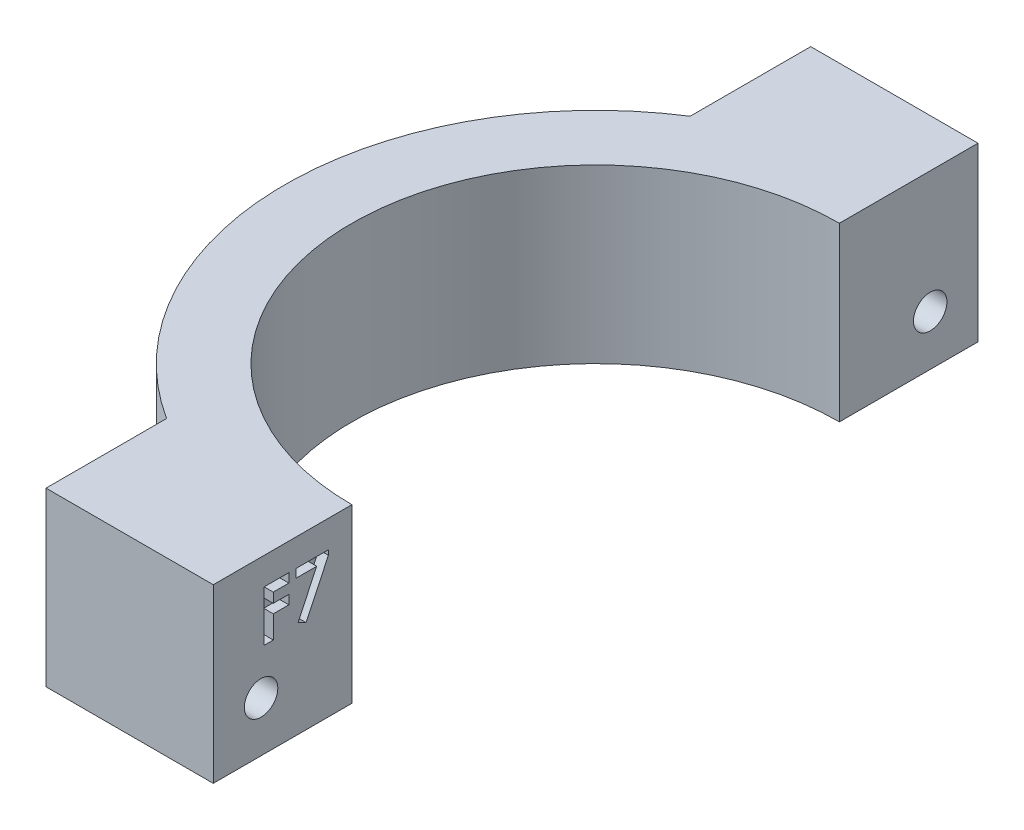
SolidWorks part; units mm, degrees
ref_plane "Front Plane" through (0, 0, 0) normal (0, 0, 1) x (1, 0, 0)
ref_plane "Top Plane" through (0, 0, 0) normal (0, 1, 0) x (1, 0, 0)
ref_plane "Right Plane" through (0, 0, 0) normal (1, 0, 0) x (0, 0, -1)
sketch "Sketch1" plane through (0, 0, 0) normal (0, 1, 0) x (1, 0, 0)
  line L0 (-46.9983, 32.5286) -> (-46.9983, -47.4714)
  line L1 (-46.9983, -47.4714) -> (-11.9983, -47.4714)
  line L2 (-11.9983, -47.4714) -> (-11.9983, -32.9714)
  line L3 (-46.9983, 32.5286) -> (-11.9983, 32.5286)
  line L4 (-11.9983, 32.5286) -> (-11.9983, 18.0286)
  line L5 (-29.4983, 32.5286) -> (-29.4983, 19.9147)
  line L6 (-29.4983, -47.4714) -> (-29.4983, -34.8576)
  arc A0 (-11.9983, 18.0286) -> (-11.9983, -32.9714) centre (-11.9983, -7.4714) ccw
  arc A1 (-11.9983, 25.0286) -> (-11.9983, -39.9714) centre (-11.9983, -7.4714) ccw
  dimension "D1" = 80
  dimension "D2" = 35
  dimension "D3" = 35
  dimension "D4" = 51
  dimension "D5" = 14.5
  dimension "D6" = 14.5
  dimension "D7" = 7
extrude "Boss-Extrude1" add sketch "Sketch1" along normal blind 18 contours A1 L4 L3 L5 | L4 A1 L2 A0 | A1 L6 L1 L2
sketch "Sketch2" plane through (-11.9983, 0, 0) normal (1, 0, 0) x (0, 0, -1)
  line L0 (-47.4714, 18) -> (-32.9714, 18) construction
  line L3 (32.5286, 18) -> (18.0286, 18) construction
  circle A0 centre (-42.4714, 5.25) radius 1.75
  circle A1 centre (27.5286, 5.25) radius 1.75
  dimension "D3" = 3.5
  dimension "D4" = 3.5
  dimension "D1" = 12.75
  dimension "D2" = 12.75
extrude "Cut-Extrude1" cut sketch "Sketch2" against normal through all
sketch "Sketch3" plane through (-11.9983, 0, 0) normal (1, 0, 0) x (0, 0, -1)
  text T0 "<b>F7</b>" font "Century Gothic" height in points 20
extrude "Cut-Extrude2" cut sketch "Sketch3" against normal blind 1
sketch "Sketch4" plane through (-29.4983, 0, 0) normal (-1, 0, 0) x (0, 0, 1)
  line L1 (45.042, 3.3858) -> (45.3712, 6.5441)
  line L2 (45.3712, 6.5441) -> (42.8006, 8.4083)
  line L3 (42.8006, 8.4083) -> (39.9008, 7.1142)
  line L4 (39.9008, 7.1142) -> (39.5717, 3.9559)
  line L5 (39.5717, 3.9559) -> (42.1422, 2.0917)
  line L6 (42.1422, 2.0917) -> (45.042, 3.3858)
  line L7 (-25.2832, 3.0046) -> (-24.4613, 6.0719)
  line L8 (-24.4613, 6.0719) -> (-26.7067, 8.3172)
  line L9 (-26.7067, 8.3172) -> (-29.7739, 7.4954)
  line L10 (-29.7739, 7.4954) -> (-30.5958, 4.4281)
  line L11 (-30.5958, 4.4281) -> (-28.3504, 2.1828)
  line L12 (-28.3504, 2.1828) -> (-25.2832, 3.0046)
  circle A0 centre (42.4714, 5.25) radius 2.75 construction
  circle A1 centre (-27.5286, 5.25) radius 2.75 construction
extrude "Cut-Extrude3" cut sketch "Sketch4" against normal blind 5
